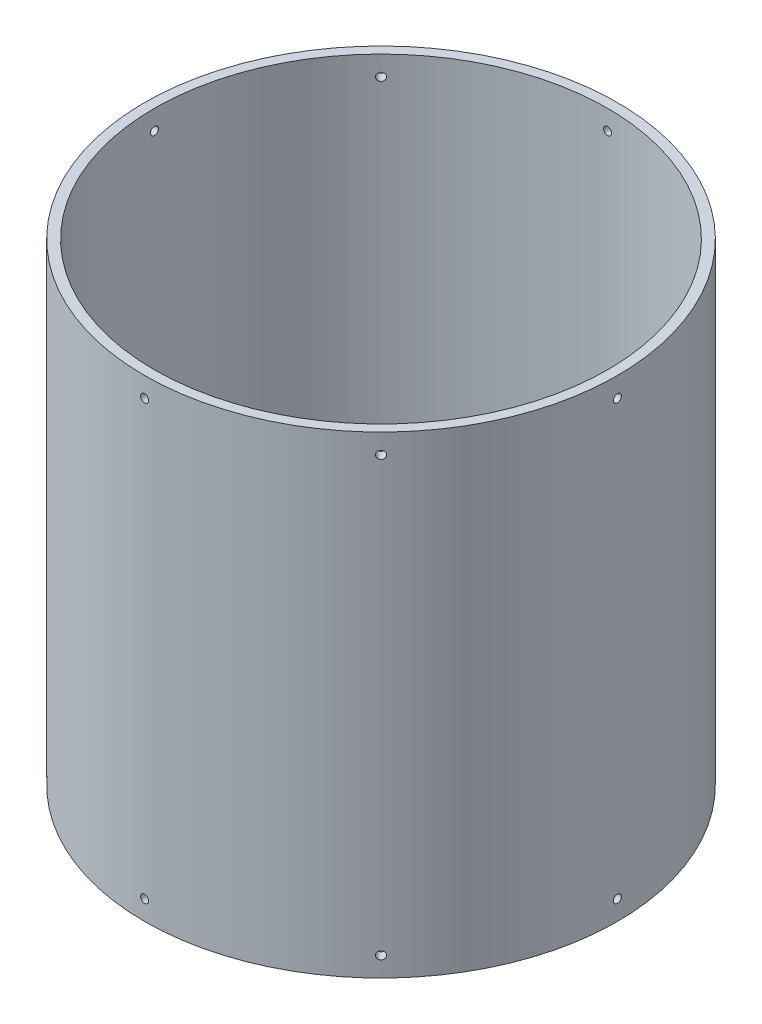
SolidWorks part; units mm, degrees
material "E-Glass Fiber"
ref_plane "Front Plane" through (0, 0, 0) normal (0, 0, 1) x (1, 0, 0)
ref_plane "Top Plane" through (0, 0, 0) normal (0, 1, 0) x (1, 0, 0)
ref_plane "Right Plane" through (0, 0, 0) normal (1, 0, 0) x (0, 0, -1)
sketch "Sketch1" plane through (0, 0, 0) normal (0, 1, 0) x (1, 0, 0)
  circle A0 centre (0, 0) radius 152.4
  circle A1 centre (0, 0) radius 146.05
  dimension "D1" = 304.8
  dimension "D2" = 292.1
extrude "Boss-Extrude1" add sketch "Sketch1" along normal blind 304.8
ref_plane "Plane1" through (152.4, 0, 0) normal (1, 0, 0) x (0, 0, -1)
sketch "Sketch2" plane through (152.4, 0, 0) normal (1, 0, 0) x (0, 0, -1)
  line L0 (0, 323.4357) -> (0, -45.9614) construction
  line L1 (-152.4, 0) -> (152.4, 0) construction
  line L2 (152.4, 304.8) -> (-152.4, 304.8) construction
  line L3 (-152.4, 0) -> (152.4, 0) construction
  line L4 (152.4, 304.8) -> (-152.4, 304.8) construction
hole_wizard "#10 Clearance Hole1" positions "3DSketch1" profile "Sketch3" hole size "#10" standard "ANSI Inch"
sketch3d "3DSketch1"
  line L0 (152.4, 323.4357, 0) -> (152.4, -45.9614, 0) construction
  line L1 (152.4, 304.8, -152.4) -> (152.4, 304.8, 152.4) construction
  line L2 (152.4, 0, 152.4) -> (152.4, 0, -152.4) construction
  point P0 (152.4, 292.1, 0)
  point P2 (152.4, 12.7, 0)
  dimension "D1" = 12.7
  dimension "D2" = 12.7
sketch "Sketch3" plane through (152.4, 292.1, 0) normal (0, 1, 0) x (0, 0, -1)
  line L0 (0, 0) -> (0, 358.9473)
  line L1 (0, 358.9473) -> (2.5527, 358.9473)
  line L2 (2.5527, 358.9473) -> (2.5527, 0)
  line L5 (2.5527, 0) -> (0, 0)
  line L11 (0, -6.35) -> (0, 107.95) construction
  dimension "Thru Hole Dia." = 5.1054
  dimension "Thru Hole Depth" = 358.9473
pattern_circular "CirPattern1" count 8 over 360 about axis through (0, 304.8, 0) along (0, -1, 0) of "#10 Clearance Hole1"
